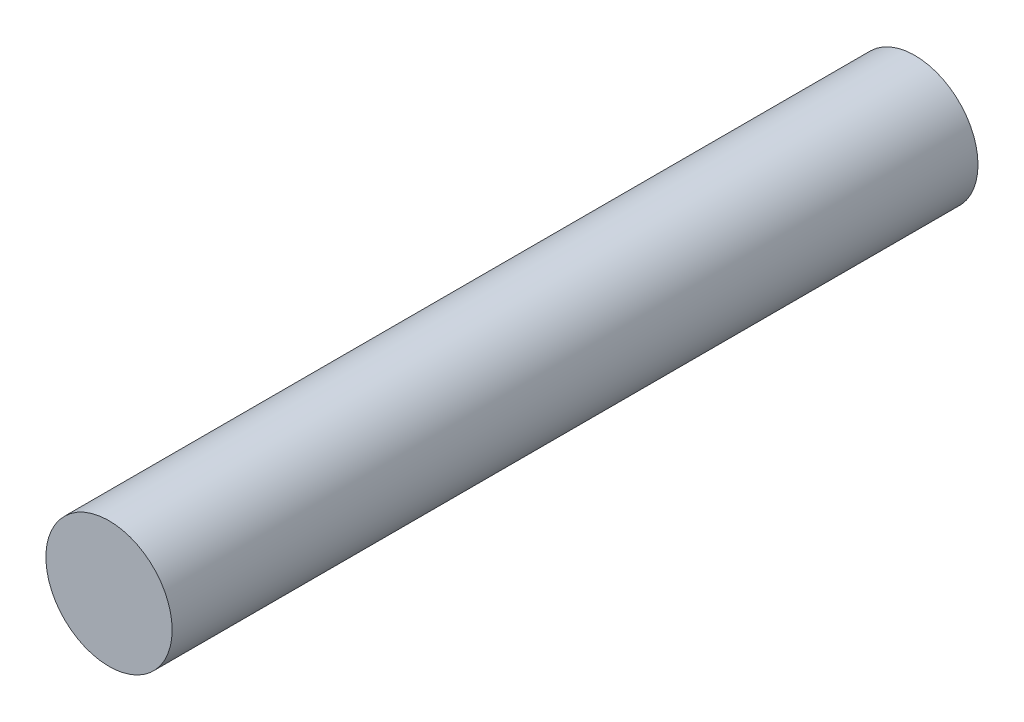
SolidWorks part; units mm, degrees
ref_plane "Face" through (0, 0, 0) normal (0, 0, 1) x (1, 0, 0)
ref_plane "Dessus" through (0, 0, 0) normal (0, 1, 0) x (1, 0, 0)
ref_plane "Droite" through (0, 0, 0) normal (1, 0, 0) x (0, 0, -1)
sketch "Esquisse1" plane through (0, 0, 0) normal (0, 0, 1) x (1, 0, 0)
  circle A0 centre (0, 0) radius 4.7
extrude "Extrusion1" add sketch "Esquisse1" along normal blind 60
